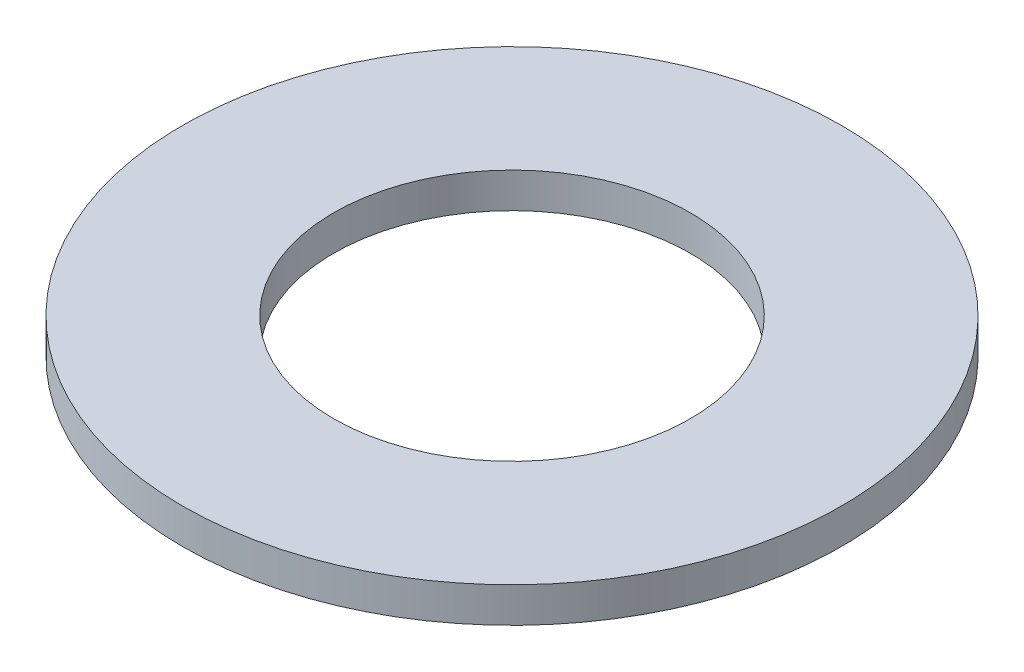
SolidWorks part; units mm, degrees
ref_plane "Front Plane" through (0, 0, 0) normal (0, 0, 1) x (1, 0, 0)
ref_plane "Top Plane" through (0, 0, 0) normal (0, 1, 0) x (1, 0, 0)
ref_plane "Right Plane" through (0, 0, 0) normal (1, 0, 0) x (0, 0, -1)
sketch "Sketch1" plane through (0, 0, 0) normal (0, 1, 0) x (1, 0, 0)
  circle A0 centre (0, 0) radius 9.525
  dimension "OD" = 19.05
extrude "Boss-Extrude1" add sketch "Sketch1" along normal blind 1.016
sketch "Sketch5" plane through (0, 1.016, 0) normal (0, 1, 0) x (-1, 0, 0)
  circle A0 centre (0, 0) radius 5.1562
  dimension "ID" = 10.3124
extrude "Cut-Extrude1" cut sketch "Sketch5" against normal through all
